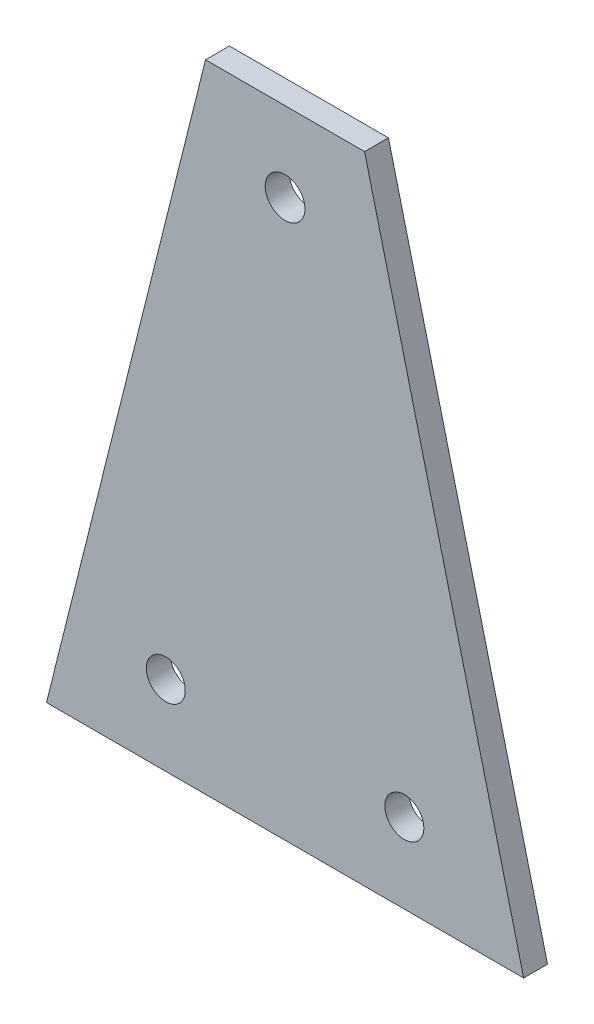
SolidWorks part; units mm, degrees
ref_plane "Front Plane" through (0, 0, 0) normal (0, 0, 1) x (1, 0, 0)
ref_plane "Top Plane" through (0, 0, 0) normal (0, 1, 0) x (1, 0, 0)
ref_plane "Right Plane" through (0, 0, 0) normal (1, 0, 0) x (0, 0, -1)
sketch "Sketch1" plane through (0, 0, 0) normal (0, 0, 1) x (1, 0, 0)
  line L0 (-10, 0) -> (10, 0)
  line L1 (10, 0) -> (30, -80)
  line L2 (30, -80) -> (-30, -80)
  line L3 (0, -55) -> (0, 55) construction
  line L4 (-10, 0) -> (-30, -80)
  circle A0 centre (0, -10) radius 2.5
  circle A2 centre (15, -69.97) radius 2.45
  circle A3 centre (-15, -69.97) radius 2.45
  point P9 (0, -80)
  point P10 (0, 0)
  dimension "D4" = 5
  dimension "D5" = 4.9
  dimension "D7" = 10
  dimension "D8" = 10.03
  dimension "D1" = 10
  dimension "D2" = 30
  dimension "D3" = 80
  dimension "D6" = 15
extrude "Boss-Extrude1" add sketch "Sketch1" along normal blind 3
